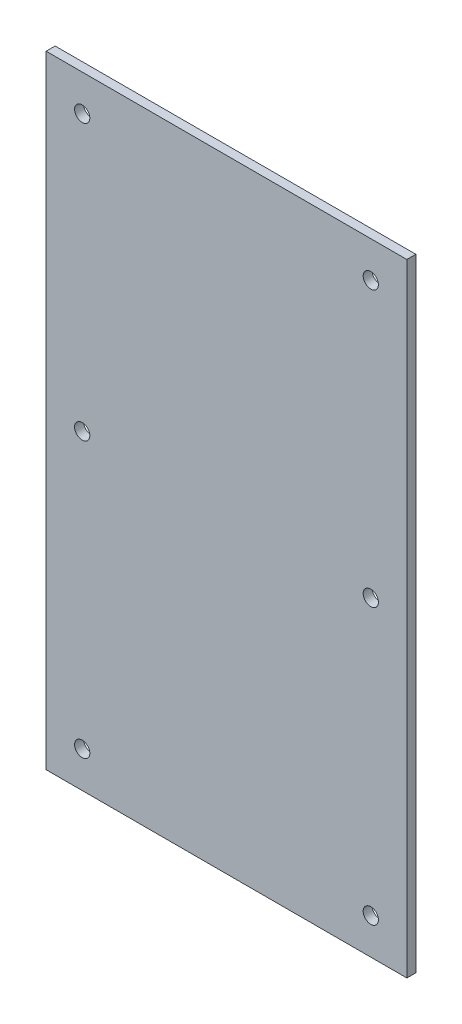
SolidWorks part; units mm, degrees
ref_plane "Front Plane" through (0, 0, 0) normal (0, 0, 1) x (1, 0, 0)
ref_plane "Top Plane" through (0, 0, 0) normal (0, 1, 0) x (1, 0, 0)
ref_plane "Right Plane" through (0, 0, 0) normal (1, 0, 0) x (0, 0, -1)
sketch "Sketch1" plane through (0, 0, 0) normal (0, 0, 1) x (1, 0, 0)
  line L1 (-127, 219.075) -> (127, 219.075)
  line L2 (-127, 219.075) -> (-127, -219.075)
  line L3 (-127, -219.075) -> (127, -219.075)
  line L4 (127, 219.075) -> (127, -219.075)
  line L5 (-127, 219.075) -> (127, -219.075) construction
  line L6 (-127, -219.075) -> (127, 219.075) construction
  point P0 (0, 0)
  dimension "D1" = 438.15
  dimension "D2" = 254
extrude "Boss-Extrude1" add sketch "Sketch1" along normal blind 6.35
hole_wizard "27/64 (0.42188) Diameter Hole1" positions "Sketch2" profile "Sketch3" hole size "27/64" standard "ANSI Inch" end condition through all
sketch "Sketch2" plane through (0, 0, 6.35) normal (0, 0, 1) x (1, 0, 0)
  line L0 (-127, 0) -> (127, 0) construction
  line L1 (-127, 219.075) -> (-127, -219.075) construction
  line L2 (127, -219.075) -> (127, 219.075) construction
  line L4 (0, 219.075) -> (0, -219.075) construction
  line L5 (127, 219.075) -> (-127, 219.075) construction
  line L6 (-127, -219.075) -> (127, -219.075) construction
  point P0 (-101.6, 193.675)
  point P4 (-101.6, 0)
  point P23 (-101.6, -193.675)
  point P24 (101.6, 193.675)
  point P25 (101.6, 0)
  point P26 (101.6, -193.675)
  dimension "D1" = 25.4
  dimension "D2" = 25.4
sketch "Sketch3" plane through (-101.6, 193.675, 6.35) normal (1, 0, 0) x (0, -1, 0)
  line L0 (0, 0) -> (0, 6.35)
  line L1 (0, 6.35) -> (5.3579, 6.35)
  line L2 (5.3579, 6.35) -> (5.3579, 0)
  line L5 (5.3579, 0) -> (0, 0)
  line L11 (0, -6.35) -> (0, 107.95) construction
  dimension "Thru Hole Dia." = 10.7158
  dimension "Thru Hole Depth" = 6.35
